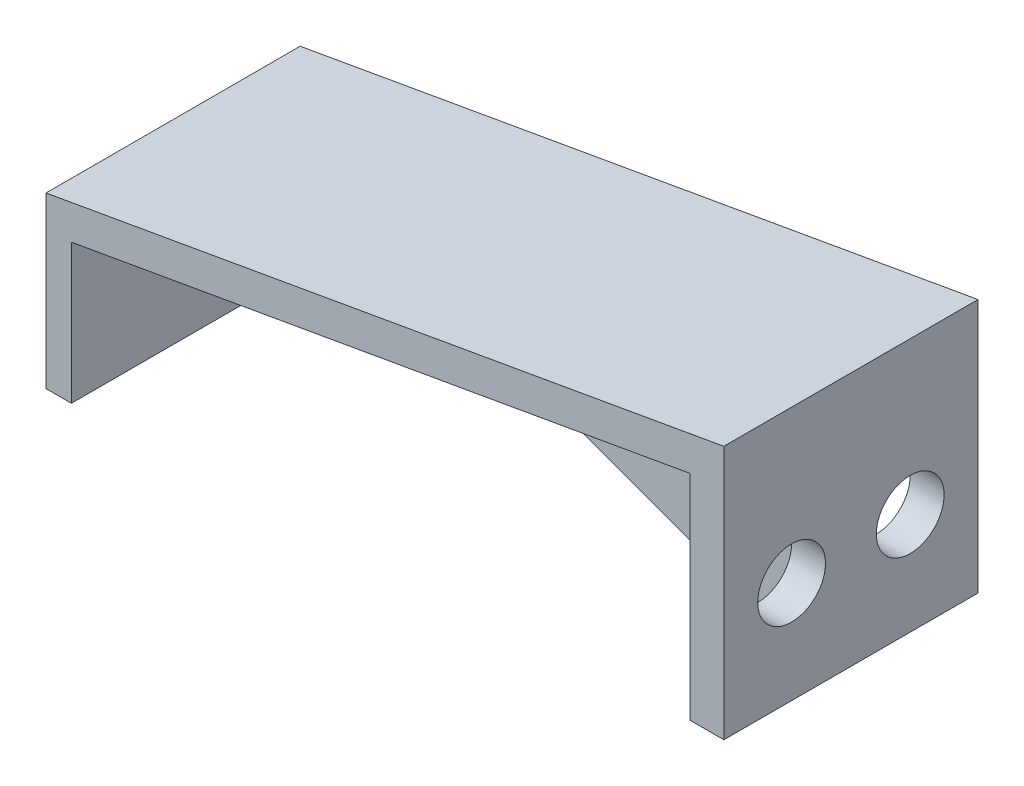
SolidWorks part; units mm, degrees
ref_plane "Front Plane" through (0, 0, 0) normal (0, 0, 1) x (1, 0, 0)
ref_plane "Top Plane" through (0, 0, 0) normal (0, 1, 0) x (1, 0, 0)
ref_plane "Right Plane" through (0, 0, 0) normal (1, 0, 0) x (0, 0, -1)
sketch "Sketch1" plane through (0, 0, 0) normal (0, 0, 1) x (1, 0, 0)
  line L0 (-477.5874, 0) -> (23401.7807, 0) construction
  line L1 (0, -477.5874) -> (0, 23401.7807) construction
  line L2 (0, 0) -> (0, 10)
  line L3 (0, 10) -> (40, 17.0531)
  line L4 (40, 17.0531) -> (40, 2.0531)
  line L5 (40, 2.0531) -> (38, 2.0531)
  line L6 (38, 2.0531) -> (38, 14.6696)
  line L7 (38, 14.6696) -> (1.5, 8.2336)
  line L8 (1.5, 8.2336) -> (1.5, 0)
  line L9 (1.5, 0) -> (0, 0)
  dimension "D1" = 2
  dimension "D2" = 2
  dimension "D3" = 1.5
  dimension "D4" = 15
  dimension "D5" = 10
  dimension "D6" = 80
  dimension "D7" = 40
extrude "Boss-Extrude1" add sketch "Sketch1" along normal blind 15
ref_plane "Plane1" through (0, 0, 7.5) normal (0, 0, -1) x (-1, 0, 0)
sketch "Sketch5" plane through (0, 0, 7.5) normal (0, 0, -1) x (-1, 0, 0)
  line L0 (-38, 14.6696) -> (-38, 2.0531)
  line L1 (-38, 2.0531) -> (-14.649, 10.5522)
  line L2 (-1.5, 8.2336) -> (-38, 14.6696) construction
  line L3 (-14.649, 10.5522) -> (-38, 14.6696)
  dimension "D1" = 70
extrude "Boss-Extrude2" add sketch "Sketch5" along normal mid plane 1.5
sketch "Sketch6" plane through (40, 0, 0) normal (1, 0, 0) x (0, 0, -1)
  line L0 (-7.5, -9.3792) -> (-7.5, 9.3792) construction
  circle A0 centre (-4, 8.0693) radius 2
  circle A1 centre (-11, 8.0693) radius 2
  dimension "D1" = 3.5
  dimension "D2" = 4
extrude "Cut-Extrude1" cut sketch "Sketch6" against normal blind 2
sketch "Sketch7" plane through (0, 0, 0) normal (-1, 0, 0) x (0, 0, 1)
  line L0 (7.5, 9.3792) -> (7.5, -9.3792) construction
  line L1 (15, 0) -> (0, 0) construction
  circle A0 centre (7.5, 5) radius 2
  dimension "D1" = 4
  dimension "D2" = 5
extrude "Cut-Extrude2" cut sketch "Sketch7" against normal blind 1.5
